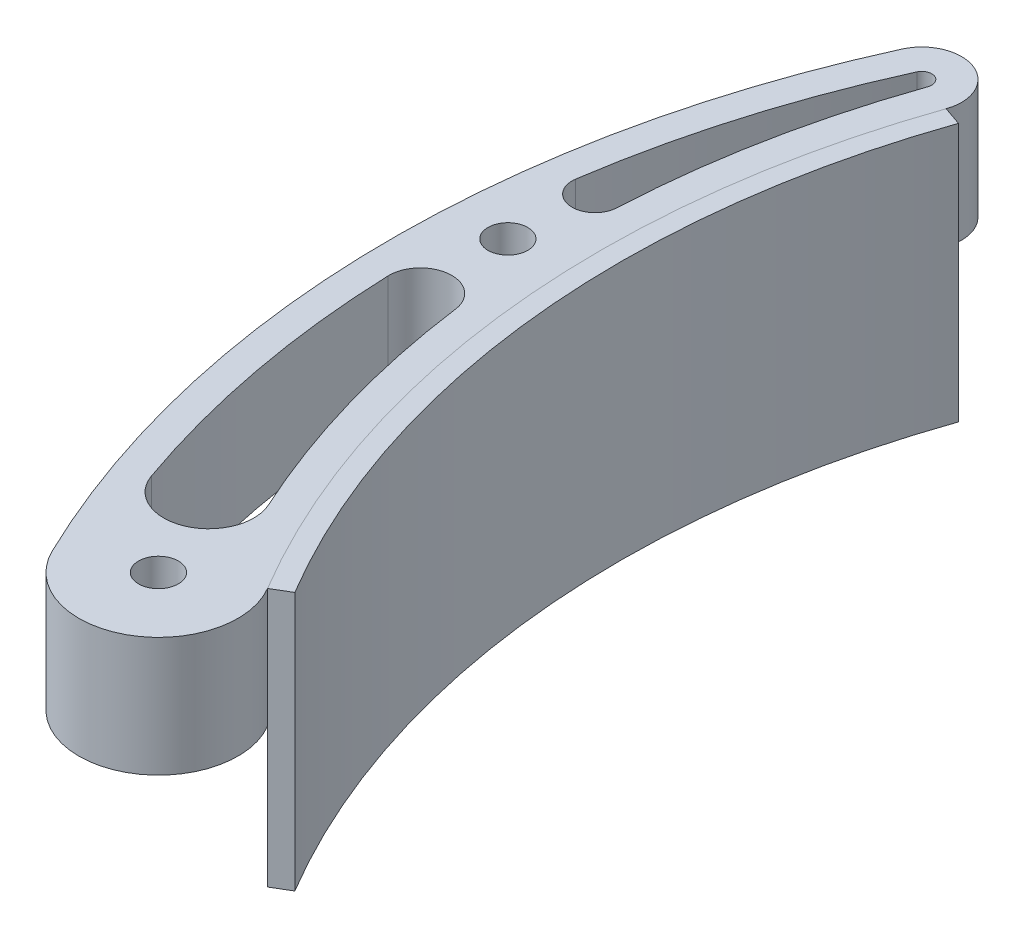
SolidWorks part; units mm, degrees
material "6061-T6 (SS)"
ref_plane "Front Plane" through (0, 0, 0) normal (0, 0, 1) x (1, 0, 0)
ref_plane "Top Plane" through (0, 0, 0) normal (0, 1, 0) x (1, 0, 0)
ref_plane "Right Plane" through (0, 0, 0) normal (1, 0, 0) x (0, 0, -1)
sketch "Sketch1" plane through (0, 0, 0) normal (0, 1, 0) x (1, 0, 0)
  line L5 (-134.0196, -92.456) -> (-46.5467, -92.456) construction
  line L6 (0, -143.256) -> (-105.4914, -143.256) construction
  circle A0 centre (0, 0) radius 143.256 construction
  arc A1 (-135.2523, 47.2132) -> (-123.106, -73.2612) centre (0, 0) ccw
  circle A2 centre (-134.0196, -79.756) radius 3.175
  arc A3 (-123.106, -73.2612) -> (-145.4546, -85.2815) centre (-134.0196, -79.756) cw
  arc A4 (-145.4546, -85.2815) -> (-147.0269, 51.937) centre (0, -14.9966) cw
  arc A5 (-147.0269, 51.937) -> (-135.2523, 47.2132) centre (-141.2476, 49.306) cw
  circle A6 centre (-152.2388, -5.7661) radius 3.175
  circle A7 centre (-152.2388, -5.7661) radius 12.7 construction
  arc A8 (-141.2476, 49.306) -> (-134.0196, -79.756) centre (0, -7.517) ccw construction
  dimension "D1" = 286.512
  dimension "D2" = 6.35
  dimension "D3" = 12.7
  dimension "D4" = 6.35
  dimension "D6" = 6.35
  dimension "D7" = 9.525
  dimension "D5" = 63.5
  dimension "D10" = 50
  dimension "D11" = 76.2
extrude "Boss-Extrude1" add sketch "Sketch1" along normal blind 19.05
sketch "Sketch2" plane through (0, 19.05, 0) normal (0, 1, 0) x (1, 0, 0)
  arc A0 (-142.6924, 49.9638) -> (-139.7487, 48.7828) centre (-141.2476, 49.306) cw
  arc A1 (-147.8428, 7.2096) -> (-155.0992, 7.9209) centre (-151.4884, 7.3874) cw
  circle A2 centre (-152.2388, -5.7661) radius 9.525 construction
  circle A3 centre (-152.2388, -5.7661) radius 3.175 construction
  arc A8 (-139.7487, 48.7828) -> (-127.1986, -75.6968) centre (0, 0) ccw
  arc A9 (-139.7487, 48.7828) -> (-147.8428, 7.2096) centre (0, 0) ccw
  arc A11 (-142.6924, 49.9638) -> (-141.1665, -83.2094) centre (0, -14.9966) ccw
  arc A12 (-142.6924, 49.9638) -> (-155.0992, 7.9209) centre (0, -14.9966) ccw
  dimension "D3" = 6.35
  dimension "D1" = 4.7625
  dimension "D2" = 4.7625
extrude "Cut-Extrude1" cut sketch "Sketch2" against normal through all
sketch "Sketch3" plane through (0, 19.05, 0) normal (0, 1, 0) x (1, 0, 0)
  line L0 (-152.2388, -5.7661) -> (-151.679, -20.2922) construction
  line L1 (-141.1195, -64.6207) -> (-134.0196, -79.756) construction
  circle A0 centre (-152.2388, -5.7661) radius 3.175 construction
  circle A1 centre (-134.0196, -79.756) radius 3.175 construction
  arc A5 (-139.7487, 48.7828) -> (-127.1986, -75.6968) centre (0, 0) ccw
  arc A6 (-146.7114, -19.6276) -> (-134.5797, -61.6261) centre (0, 0) ccw
  arc A7 (-156.6877, -20.467) -> (-146.7114, -19.6276) centre (-151.679, -20.2922) cw
  arc A8 (-142.6924, 49.9638) -> (-141.1665, -83.2094) centre (0, -14.9966) ccw
  arc A9 (-156.6877, -20.467) -> (-147.905, -67.0068) centre (0, -14.9966) ccw
  arc A10 (-147.905, -67.0068) -> (-134.5797, -61.6261) centre (-141.1195, -64.6207) ccw
  point P12 (-151.872, -15.2841)
  point P17 (-152.1165, -8.9388)
  point P18 (-138.0648, -71.1327)
  point P21 (-135.368, -76.8816)
  dimension "D3" = 6.35
  dimension "D4" = 6.35
  dimension "D1" = 4.7625
  dimension "D2" = 4.7625
extrude "Cut-Extrude2" cut sketch "Sketch3" against normal through all
sketch "Sketch4" plane through (0, 19.05, 0) normal (0, 1, 0) x (1, 0, 0)
  line L0 (-135.2523, 47.2132) -> (-132.2547, 46.1668)
  line L1 (-123.106, -73.2612) -> (-120.3775, -71.6375)
  arc A0 (-135.2523, 47.2132) -> (-123.106, -73.2612) centre (0, 0) ccw
  arc A1 (-135.2523, 47.2132) -> (-123.106, -73.2612) centre (0, 0) ccw construction
  arc A2 (-132.2547, 46.1668) -> (-120.3775, -71.6375) centre (0, 0) ccw
  circle A3 centre (-134.0196, -79.756) radius 3.175 construction
  point P10 (-141.2476, 49.306)
  point P11 (-134.0196, -79.756)
  dimension "D1" = 3.175
extrude "Boss-Extrude2" add sketch "Sketch4" against normal blind 41.275 separate body
